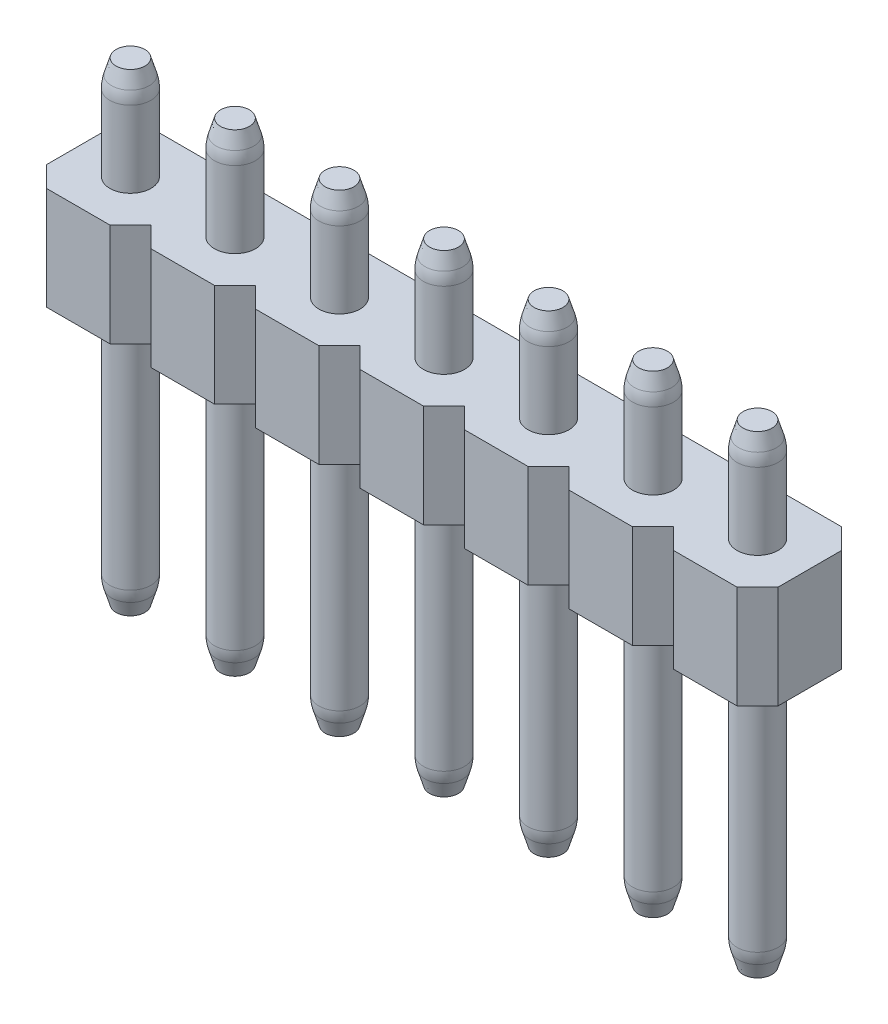
SolidWorks part; units mm, degrees
material "Brass"
ref_plane "Front Plane" through (0, 0, 0) normal (0, 0, 1) x (1, 0, 0)
ref_plane "Top Plane" through (0, 0, 0) normal (0, 1, 0) x (1, 0, 0)
ref_plane "Right Plane" through (0, 0, 0) normal (1, 0, 0) x (0, 0, -1)
sketch "Sketch1" plane through (0, 0, 0) normal (0, 1, 0) x (1, 0, 0)
  line L0 (0, 0) -> (2.54, 0) construction
  circle A0 centre (0, 0) radius 0.5
  circle A1 centre (2.54, 0) radius 0.5
  circle A2 centre (5.08, 0) radius 0.5
  circle A3 centre (7.62, 0) radius 0.5
  circle A4 centre (10.16, 0) radius 0.5
  circle A5 centre (12.7, 0) radius 0.5
  circle A6 centre (15.24, 0) radius 0.5
  circle A7 centre (17.78, 0) radius 0.5
  circle A8 centre (20.32, 0) radius 0.5
  circle A9 centre (22.86, 0) radius 0.5
  circle A10 centre (25.4, 0) radius 0.5
  circle A11 centre (27.94, 0) radius 0.5
  circle A12 centre (30.48, 0) radius 0.5
  circle A13 centre (33.02, 0) radius 0.5
  circle A14 centre (35.56, 0) radius 0.5
  circle A15 centre (38.1, 0) radius 0.5
  dimension "D1" = 1
  dimension "D3" = 2.54
  dimension "D2" = 16
extrude "Boss-Extrude1" add sketch "Sketch1" along normal blind 11.5
ref_plane "Plane1" through (0, 6.5, 0) normal (0, 1, 0) x (1, 0, 0)
sketch "Sketch2" plane through (0, 6.5, 0) normal (0, 1, 0) x (1, 0, 0)
  line L0 (-1.27, 0.77) -> (-0.77, 1.27)
  line L1 (-0.77, -1.27) -> (0.77, -1.27)
  line L2 (-1.27, -0.77) -> (-1.27, 0.77)
  line L3 (-0.77, 1.27) -> (0.77, 1.27)
  line L5 (-1.27, -1.27) -> (1.27, 1.27) construction
  line L6 (-1.27, 1.27) -> (1.27, -1.27) construction
  line L7 (0.77, 1.27) -> (1.27, 0.77)
  line L8 (0.77, -1.27) -> (1.27, -0.77)
  line L9 (-1.27, -0.77) -> (-0.77, -1.27)
  line L10 (1.27, 0.77) -> (1.77, 1.27)
  line L11 (1.77, 1.27) -> (3.31, 1.27)
  line L12 (3.31, 1.27) -> (3.81, 0.77)
  line L14 (3.31, -1.27) -> (3.81, -0.77)
  line L15 (1.77, -1.27) -> (3.31, -1.27)
  line L16 (1.27, -0.77) -> (1.77, -1.27)
  line L17 (3.81, 0.77) -> (4.31, 1.27)
  line L18 (4.31, 1.27) -> (5.85, 1.27)
  line L19 (5.85, 1.27) -> (6.35, 0.77)
  line L20 (6.35, -0.77) -> (6.35, 0.77) construction
  line L21 (5.85, -1.27) -> (6.35, -0.77)
  line L22 (4.31, -1.27) -> (5.85, -1.27)
  line L23 (3.81, -0.77) -> (4.31, -1.27)
  line L24 (6.35, 0.77) -> (6.85, 1.27)
  line L25 (6.85, 1.27) -> (8.39, 1.27)
  line L26 (8.39, 1.27) -> (8.89, 0.77)
  line L27 (8.89, -0.77) -> (8.89, 0.77) construction
  line L28 (8.39, -1.27) -> (8.89, -0.77)
  line L29 (6.85, -1.27) -> (8.39, -1.27)
  line L30 (6.35, -0.77) -> (6.85, -1.27)
  line L31 (8.89, 0.77) -> (9.39, 1.27)
  line L32 (9.39, 1.27) -> (10.93, 1.27)
  line L33 (10.93, 1.27) -> (11.43, 0.77)
  line L34 (11.43, -0.77) -> (11.43, 0.77) construction
  line L35 (10.93, -1.27) -> (11.43, -0.77)
  line L36 (9.39, -1.27) -> (10.93, -1.27)
  line L37 (8.89, -0.77) -> (9.39, -1.27)
  line L38 (11.43, 0.77) -> (11.93, 1.27)
  line L39 (11.93, 1.27) -> (13.47, 1.27)
  line L40 (13.47, 1.27) -> (13.97, 0.77)
  line L41 (13.97, -0.77) -> (13.97, 0.77) construction
  line L42 (13.47, -1.27) -> (13.97, -0.77)
  line L43 (11.93, -1.27) -> (13.47, -1.27)
  line L44 (11.43, -0.77) -> (11.93, -1.27)
  line L45 (13.97, 0.77) -> (14.47, 1.27)
  line L46 (14.47, 1.27) -> (16.01, 1.27)
  line L47 (16.01, 1.27) -> (16.51, 0.77)
  line L48 (16.51, -0.77) -> (16.51, 0.77) construction
  line L49 (16.01, -1.27) -> (16.51, -0.77)
  line L50 (14.47, -1.27) -> (16.01, -1.27)
  line L51 (13.97, -0.77) -> (14.47, -1.27)
  line L52 (16.51, 0.77) -> (17.01, 1.27)
  line L53 (17.01, 1.27) -> (18.55, 1.27)
  line L54 (18.55, 1.27) -> (19.05, 0.77)
  line L55 (19.05, -0.77) -> (19.05, 0.77) construction
  line L56 (18.55, -1.27) -> (19.05, -0.77)
  line L57 (17.01, -1.27) -> (18.55, -1.27)
  line L58 (16.51, -0.77) -> (17.01, -1.27)
  line L59 (19.05, 0.77) -> (19.55, 1.27)
  line L60 (19.55, 1.27) -> (21.09, 1.27)
  line L61 (21.09, 1.27) -> (21.59, 0.77)
  line L62 (21.59, -0.77) -> (21.59, 0.77) construction
  line L63 (21.09, -1.27) -> (21.59, -0.77)
  line L64 (19.55, -1.27) -> (21.09, -1.27)
  line L65 (19.05, -0.77) -> (19.55, -1.27)
  line L66 (21.59, 0.77) -> (22.09, 1.27)
  line L67 (22.09, 1.27) -> (23.63, 1.27)
  line L68 (23.63, 1.27) -> (24.13, 0.77)
  line L69 (24.13, -0.77) -> (24.13, 0.77) construction
  line L70 (23.63, -1.27) -> (24.13, -0.77)
  line L71 (22.09, -1.27) -> (23.63, -1.27)
  line L72 (21.59, -0.77) -> (22.09, -1.27)
  line L73 (24.13, 0.77) -> (24.63, 1.27)
  line L74 (24.63, 1.27) -> (26.17, 1.27)
  line L75 (26.17, 1.27) -> (26.67, 0.77)
  line L76 (26.67, -0.77) -> (26.67, 0.77) construction
  line L77 (26.17, -1.27) -> (26.67, -0.77)
  line L78 (24.63, -1.27) -> (26.17, -1.27)
  line L79 (24.13, -0.77) -> (24.63, -1.27)
  line L80 (26.67, 0.77) -> (27.17, 1.27)
  line L81 (27.17, 1.27) -> (28.71, 1.27)
  line L82 (28.71, 1.27) -> (29.21, 0.77)
  line L83 (29.21, -0.77) -> (29.21, 0.77) construction
  line L84 (28.71, -1.27) -> (29.21, -0.77)
  line L85 (27.17, -1.27) -> (28.71, -1.27)
  line L86 (26.67, -0.77) -> (27.17, -1.27)
  line L87 (29.21, 0.77) -> (29.71, 1.27)
  line L88 (29.71, 1.27) -> (31.25, 1.27)
  line L89 (31.25, 1.27) -> (31.75, 0.77)
  line L90 (31.75, -0.77) -> (31.75, 0.77) construction
  line L91 (31.25, -1.27) -> (31.75, -0.77)
  line L92 (29.71, -1.27) -> (31.25, -1.27)
  line L93 (29.21, -0.77) -> (29.71, -1.27)
  line L94 (31.75, 0.77) -> (32.25, 1.27)
  line L95 (32.25, 1.27) -> (33.79, 1.27)
  line L96 (33.79, 1.27) -> (34.29, 0.77)
  line L97 (34.29, -0.77) -> (34.29, 0.77) construction
  line L98 (33.79, -1.27) -> (34.29, -0.77)
  line L99 (32.25, -1.27) -> (33.79, -1.27)
  line L100 (31.75, -0.77) -> (32.25, -1.27)
  line L101 (34.29, 0.77) -> (34.79, 1.27)
  line L102 (34.79, 1.27) -> (36.33, 1.27)
  line L103 (36.33, 1.27) -> (36.83, 0.77)
  line L104 (36.83, -0.77) -> (36.83, 0.77) construction
  line L105 (36.33, -1.27) -> (36.83, -0.77)
  line L106 (34.79, -1.27) -> (36.33, -1.27)
  line L107 (34.29, -0.77) -> (34.79, -1.27)
  line L108 (36.83, 0.77) -> (37.33, 1.27)
  line L109 (37.33, 1.27) -> (38.87, 1.27)
  line L110 (38.87, 1.27) -> (39.37, 0.77)
  line L111 (39.37, -0.77) -> (39.37, 0.77)
  line L112 (38.87, -1.27) -> (39.37, -0.77)
  line L113 (37.33, -1.27) -> (38.87, -1.27)
  line L114 (36.83, -0.77) -> (37.33, -1.27)
  line L115 (-1.27, 0.77) -> (1.27, 0.77) construction
  point P0 (0, 0)
  dimension "D1" = 2.54
  dimension "D2" = 2.54
  dimension "D4" = 2.54
  dimension "D3" = 16
extrude "Boss-Extrude2" add sketch "Sketch2" along normal blind 2.5
chamfer "Chamfer1" distance 0.5 distance2 0.15 16 edges at (15.24, 11.5, 0.5) (12.7, 11.5, 0.5) (10.16, 11.5, 0.5) (7.62, 11.5, 0.5) (5.08, 11.5, 0.5) (2.54, 11.5, 0.5) (0, 11.5, 0.5) (38.1, 11.5, 0.5) (35.56, 11.5, 0.5) (33.02, 11.5, 0.5) (30.48, 11.5, 0.5) (27.94, 11.5, 0.5) (25.4, 11.5, 0.5) (22.86, 11.5, 0.5) (20.32, 11.5, 0.5) (17.78, 11.5, 0.5)
fillet "Fillet1" radius 1 16 edges at (38.1, 11, 0.5) (35.56, 11, 0.5) (33.02, 11, 0.5) (30.48, 11, 0.5) (27.94, 11, 0.5) (25.4, 11, 0.5) (22.86, 11, 0.5) (20.32, 11, 0.5) (17.78, 11, 0.5) (15.24, 11, 0.5) (12.7, 11, 0.5) (10.16, 11, 0.5) (7.62, 11, 0.5) (5.08, 11, 0.5) (2.54, 11, 0.5) (0, 11, 0.5)
chamfer "Chamfer2" distance 0.15 distance2 0.5 16 edges at (10.16, 0, 0.5) (17.78, 0, 0.5) (22.86, 0, 0.5) (27.94, 0, 0.5) (30.48, 0, 0.5) (0, 0, 0.5) (2.54, 0, 0.5) (5.08, 0, 0.5) (7.62, 0, 0.5) (12.7, 0, 0.5) (15.24, 0, 0.5) (20.32, 0, 0.5) (25.4, 0, 0.5) (33.02, 0, 0.5) (35.56, 0, 0.5) (38.1, 0, 0.5)
fillet "Fillet2" radius 1 16 edges at (30.48, 0.5, 0.5) (33.02, 0.5, 0.5) (35.56, 0.5, 0.5) (38.1, 0.5, 0.5) (27.94, 0.5, 0.5) (25.4, 0.5, 0.5) (22.86, 0.5, 0.5) (20.32, 0.5, 0.5) (17.78, 0.5, 0.5) (15.24, 0.5, 0.5) (12.7, 0.5, 0.5) (10.16, 0.5, 0.5) (7.62, 0.5, 0.5) (5.08, 0.5, 0.5) (2.54, 0.5, 0.5) (0, 0.5, 0.5)
sketch "Sketch3" plane through (0, 0, 1.27) normal (0, 0, 1) x (1, 0, 0)
  line L1 (39.37, 9) -> (39.37, 6.5) construction
  line L2 (16.51, 9) -> (16.51, 6.5) construction
  line L3 (16.51, 11.5) -> (16.51, 0)
  line L4 (39.37, 11.5) -> (39.37, 0)
  line L5 (39.37, 0) -> (16.51, 0)
  line L6 (16.51, 11.5) -> (39.37, 11.5)
extrude "Cut-Extrude1" cut sketch "Sketch3" against normal through all both and the other way through all
